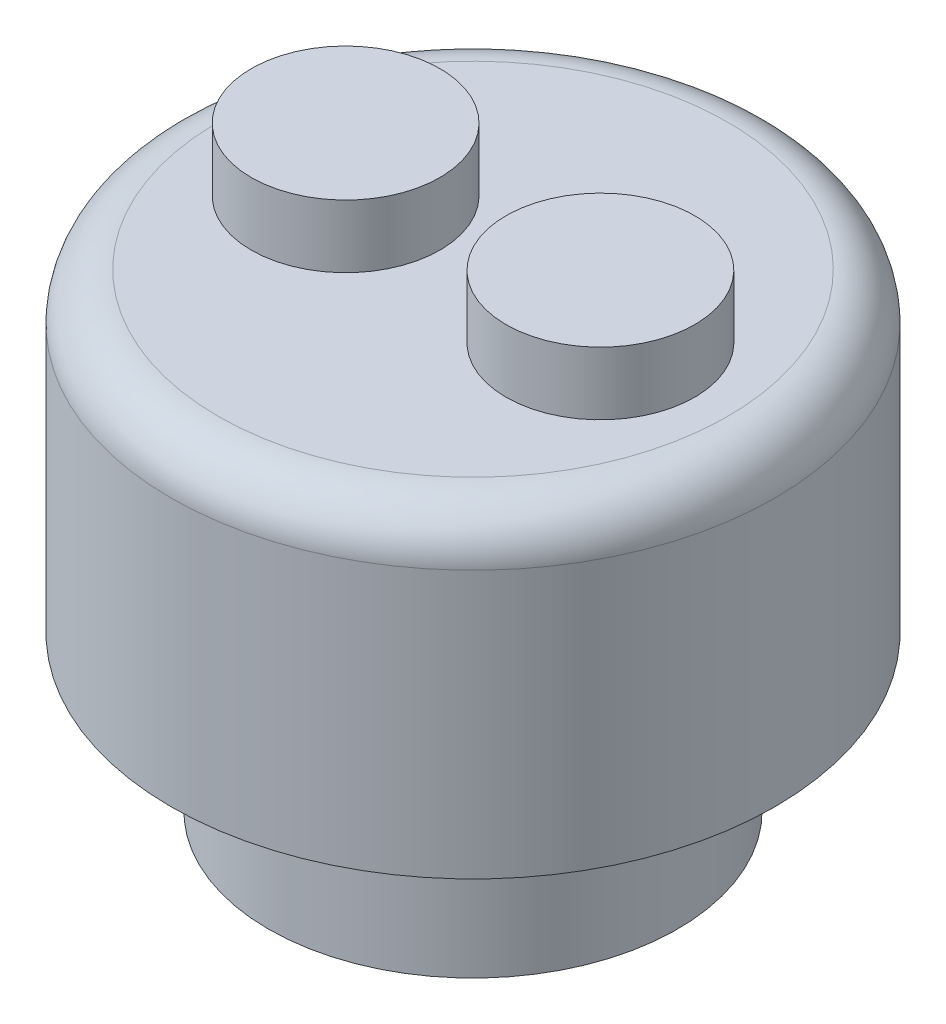
SolidWorks part; units mm, degrees
ref_plane "Front Plane" through (0, 0, 0) normal (0, 0, 1) x (1, 0, 0)
ref_plane "Top Plane" through (0, 0, 0) normal (0, 1, 0) x (1, 0, 0)
ref_plane "Right Plane" through (0, 0, 0) normal (1, 0, 0) x (0, 0, -1)
sketch "Sketch1" plane through (0, 0, 0) normal (0, 1, 0) x (1, 0, 0)
  circle A0 centre (0, 0) radius 3.25
  dimension "D1" = 6.5
extrude "Boss-Extrude1" add sketch "Sketch1" along normal blind 2.46 contours A0
sketch "Sketch2" plane through (0, 0, 0) normal (0, -1, 0) x (1, 0, 0)
  circle A1 centre (0, 0) radius 1.75
  dimension "D1" = 3.5
extrude "Cut-Extrude1" cut sketch "Sketch2" against normal blind 2.5
sketch "Sketch6" plane through (0, 2.46, 0) normal (0, 1, 0) x (1, 0, 0)
  circle A0 centre (0, 0) radius 4.8
  dimension "D1" = 9.6
extrude "Boss-Extrude2" add sketch "Sketch6" along normal blind 5 contours A0
fillet "Fillet2" radius 0.75 1 edges at (0, 7.46, 4.8)
sketch "Sketch7" plane through (0, 7.46, 0) normal (0, 1, 0) x (1, 0, 0)
  line L0 (4.05, 0) -> (0, 0) construction
  line L1 (0, 0) -> (-4.05, 0) construction
  line L2 (0, 0) -> (2.025, 0) construction
  line L3 (0, 0) -> (-2.025, 0) construction
  circle A0 centre (0, 0) radius 4.05 construction
  circle A1 centre (-2.025, 0) radius 1.5
  circle A2 centre (2.025, 0) radius 1.5
  dimension "D1" = 3
  dimension "D2" = 3
extrude "Boss-Extrude3" add sketch "Sketch7" along normal blind 1
